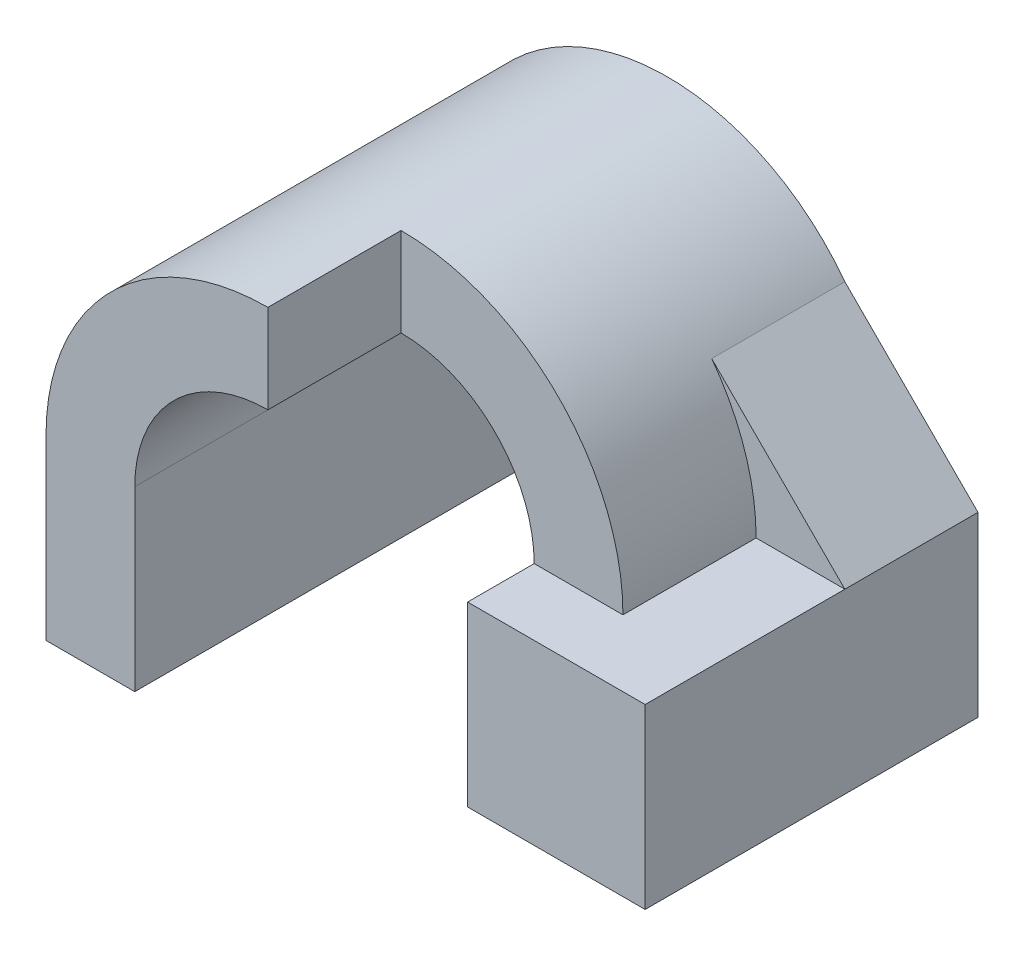
SolidWorks part; units mm, degrees
ref_plane "Front" through (0, 0, 0) normal (0, 0, 1) x (1, 0, 0)
ref_plane "Top" through (0, 0, 0) normal (0, 1, 0) x (1, 0, 0)
ref_plane "Right" through (0, 0, 0) normal (1, 0, 0) x (0, 0, -1)
sketch "Sketch1" plane through (0, 0, 0) normal (0, 0, 1) x (1, 0, 0)
  line L0 (0, 0) -> (0, -4) construction
  line L1 (3, 0) -> (3, -4)
  line L2 (-3, 0) -> (-3, -4)
  line L3 (0, 0) -> (0, -4) construction
  line L4 (5, 0) -> (5, -4)
  line L5 (-5, 0) -> (-5, -4)
  line L6 (-5, -4) -> (-3, -4)
  line L7 (3, -4) -> (5, -4)
  arc A0 (3, 0) -> (-3, 0) centre (0, 0) ccw
  arc A2 (5, 0) -> (-5, 0) centre (0, 0) ccw
  point P3 (0, -2)
  point P8 (0, -2)
  dimension "D2" = 3
  dimension "D3" = 5
  dimension "D1" = 4
extrude "Boss-Extrude1" add sketch "Sketch1" along normal blind 9
sketch "Sketch2" plane through (0, 0, 9) normal (0, 0, 1) x (1, 0, 0)
  line L1 (0, 5) -> (5, 5)
  line L2 (0, 5) -> (0, -4)
  line L3 (0, -4) -> (5, -4)
  line L4 (5, 5) -> (5, -4)
  arc A0 (5, 0) -> (-5, 0) centre (0, 0) ccw construction
extrude "Cut-Extrude1" cut sketch "Sketch2" against normal blind 3
sketch "Sketch3" plane through (0, 0, 0) normal (0, 0, -1) x (-1, 0, 0)
  line L0 (-5, -4) -> (-7, -4)
  line L1 (-7, -4) -> (-7, 0)
  line L2 (-7, 0) -> (-4, 3)
  line L3 (-5, -4) -> (-5, 0)
  arc A0 (0, 5) -> (-5, 0) centre (0, 0) ccw construction
  arc A1 (-5, 0) -> (-4, 3) centre (0, 0) cw
  dimension "D1" = 2
  dimension "D2" = 4
  dimension "D3" = 3
extrude "Boss-Extrude2" add sketch "Sketch3" against normal blind 3 separate body
sketch "Sketch4" plane through (0, 0, 3) normal (0, 0, 1) x (1, 0, 0)
  line L1 (7, 0) -> (3, 0)
  line L2 (7, 0) -> (7, -4)
  line L3 (7, -4) -> (3, -4)
  line L4 (3, 0) -> (3, -4)
extrude "Boss-Extrude3" add sketch "Sketch4" along normal blind 4.5
